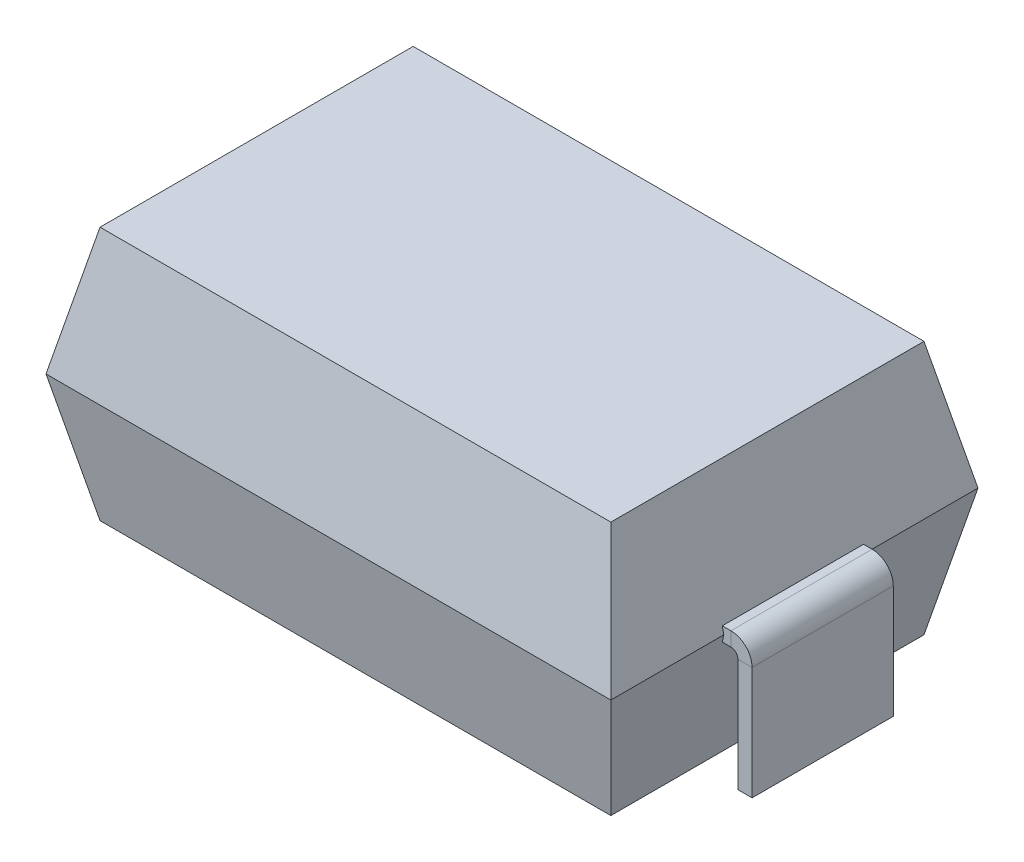
SolidWorks part; units mm, degrees
ref_plane "Front Plane" through (0, 0, 0) normal (0, 0, 1) x (1, 0, 0)
ref_plane "Top Plane" through (0, 0, 0) normal (0, 1, 0) x (1, 0, 0)
ref_plane "Right Plane" through (0, 0, 0) normal (1, 0, 0) x (0, 0, -1)
sketch "Sketch1" plane through (0, 0, 0) normal (0, 1, 0) x (1, 0, 0)
  line L1 (-2, 1.3) -> (2, 1.3)
  line L2 (-2, 1.3) -> (-2, -1.3)
  line L3 (-2, -1.3) -> (2, -1.3)
  line L4 (2, 1.3) -> (2, -1.3)
  line L5 (-2, 1.3) -> (2, -1.3) construction
  line L6 (-2, -1.3) -> (2, 1.3) construction
  point P0 (0, 0)
  dimension "D1" = 4
  dimension "D2" = 2.6
extrude "MB" add sketch "Sketch1" along normal mid plane 1.8 draft 12
sketch "Sketch2" plane through (0, 0, 0) normal (0, 0, 1) x (1, 0, 0)
  line L0 (-2.15, -0.9) -> (-2.15, -0.1)
  line L1 (-2.05, 0) -> (-2, 0)
  line L2 (-1.8087, -0.9) -> (1.8087, -0.9) construction
  arc A0 (-2.15, -0.1) -> (-2.05, 0) centre (-2.05, -0.1) cw
  dimension "D2" = 0.1
  dimension "D1" = 0.15
ref_plane "RP LEG" through (-2, 0, 0) normal (1, 0, 0) x (0, 0, -1)
sketch "Sketch3" plane through (-2, 0, 0) normal (1, 0, 0) x (0, 0, -1)
  line L1 (0.5, 0.05) -> (-0.5, 0.05)
  line L2 (0.5, 0.05) -> (0.5, -0.05)
  line L3 (0.5, -0.05) -> (-0.5, -0.05)
  line L4 (-0.5, 0.05) -> (-0.5, -0.05)
  line L5 (0.5, 0.05) -> (-0.5, -0.05) construction
  line L6 (0.5, -0.05) -> (-0.5, 0.05) construction
  point P0 (0, 0)
  dimension "D1" = 1
  dimension "D2" = 0.1
sweep "LEG" add profiles "Sketch3" path "Sketch2"
sketch "Sketch4" plane through (-2, 0, 0) normal (1, 0, 0) x (0, 0, -1)
  line L4 (-0.5, 0.05) -> (-0.5, -0.05)
  line L5 (-0.5, -0.05) -> (0.5, -0.05)
  line L6 (0.5, -0.05) -> (0.5, 0.05)
  line L7 (0.5, 0.05) -> (-0.5, 0.05)
  line L8 (-0.5, 0.05) -> (-0.5, -0.05)
  line L9 (-0.5, -0.05) -> (0.5, -0.05)
  line L10 (0.5, -0.05) -> (0.5, 0.05)
  line L11 (0.5, 0.05) -> (-0.5, 0.05)
  dimension "D1" = 0
extrude "LEG COMPLETION" add sketch "Sketch4" along normal up to next
mirror "Mirror2" about plane through (0, 0, 0) normal (1, 0, 0) of "LEG COMPLETION", "LEG"
